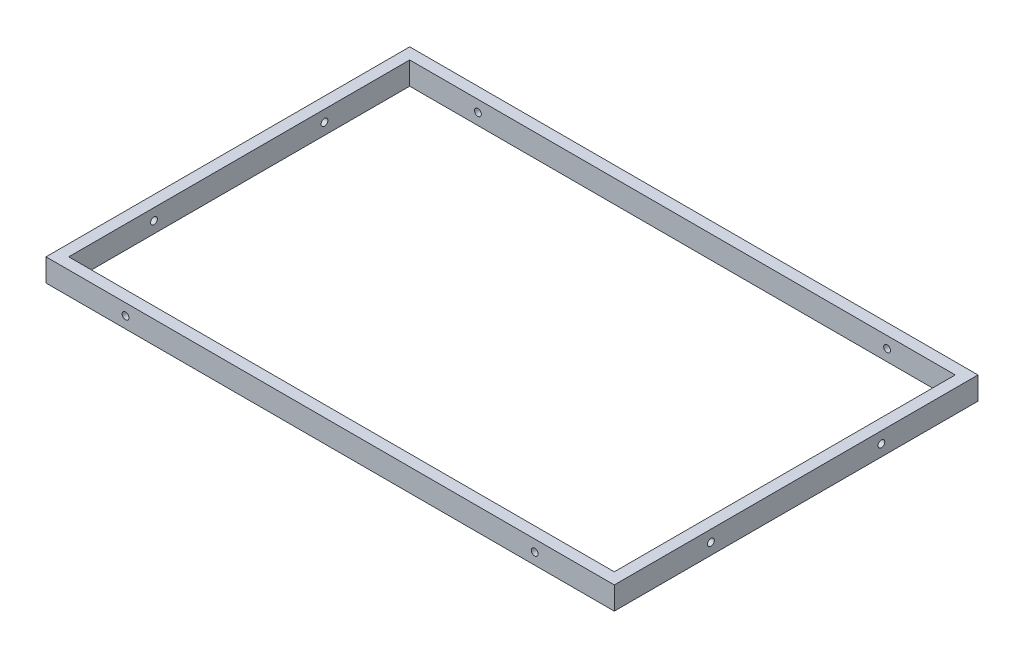
SolidWorks part; units mm, degrees
ref_plane "Front Plane" through (0, 0, 0) normal (0, 0, 1) x (1, 0, 0)
ref_plane "Top Plane" through (0, 0, 0) normal (0, 1, 0) x (1, 0, 0)
ref_plane "Right Plane" through (0, 0, 0) normal (1, 0, 0) x (0, 0, -1)
sketch "Sketch1" plane through (0, 0, 0) normal (0, 1, 0) x (1, 0, 0)
  line L0 (-250, -160) -> (-250, 160)
  line L1 (-240, -150) -> (240, -150)
  line L2 (-240, -150) -> (-240, 150)
  line L3 (-240, 150) -> (240, 150)
  line L4 (240, -150) -> (240, 150)
  line L5 (-240, -150) -> (240, 150) construction
  line L6 (-240, 150) -> (240, -150) construction
  line L7 (-250, 160) -> (250, 160)
  line L8 (250, -160) -> (250, 160)
  line L9 (-250, -160) -> (250, -160)
  point P0 (0, 0)
  dimension "D1" = 300
  dimension "D2" = 480
  dimension "D3" = 10
extrude "Boss-Extrude1" add sketch "Sketch1" along normal blind 20
sketch "Sketch2" plane through (250, 0, 0) normal (1, 0, 0) x (0, 0, -1)
  line L0 (-160, 0) -> (160, 0) construction
  circle A0 centre (75, 10) radius 3
  circle A1 centre (-75, 10) radius 3
  dimension "D5" = 6
  dimension "D6" = 6
  dimension "D1" = 75
  dimension "D2" = 75
  dimension "D3" = 10
  dimension "D4" = 10
extrude "Cut-Extrude1" cut sketch "Sketch2" against normal up to surface (500 mm away) up to face at (-250, 10, 0)
sketch "Sketch3" plane through (0, 0, 160) normal (0, 0, 1) x (1, 0, 0)
  line L0 (-250, 0) -> (250, 0) construction
  line L1 (0, 0) -> (0, -50.5068) construction
  circle A0 centre (-180, 10) radius 3
  circle A1 centre (180, 10) radius 3
  dimension "D1" = 10
  dimension "D2" = 180
extrude "Cut-Extrude2" cut sketch "Sketch3" against normal up to surface (320 mm away) up to face at (0, 10, -160)
